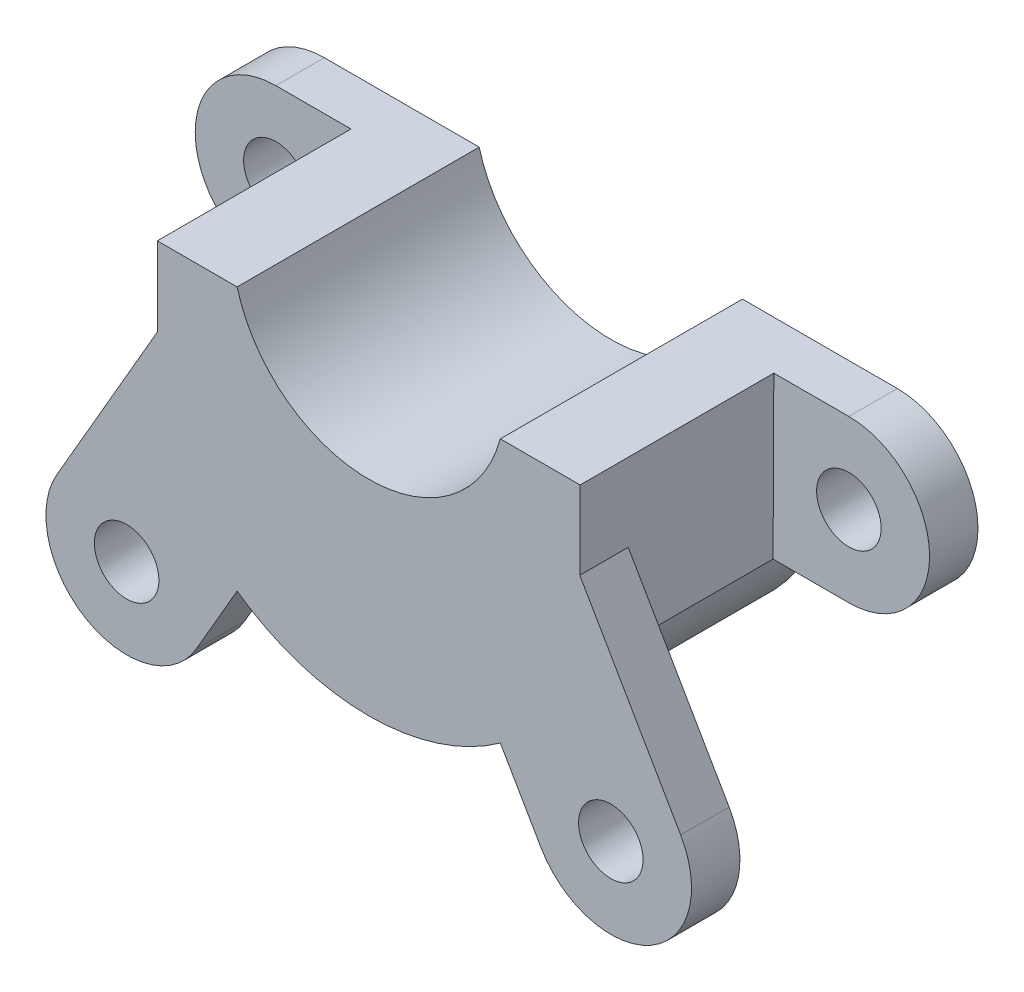
SolidWorks part; units mm, degrees
ref_plane "Plano frontal" through (0, 0, 0) normal (0, 0, 1) x (1, 0, 0)
ref_plane "Plano superior" through (0, 0, 0) normal (0, 1, 0) x (1, 0, 0)
ref_plane "Plano direito" through (0, 0, 0) normal (1, 0, 0) x (0, 0, -1)
sketch "Esboço1" plane through (0, 0, 0) normal (0, 0, 1) x (1, 0, 0)
  line L0 (-17.75, 4.941) -> (-13.0991, 4.941)
  line L1 (-17.75, -5.059) -> (-13.054, -5.059)
  line L2 (17.75, 4.941) -> (13.0991, 4.941)
  line L3 (13.054, -5.059) -> (17.75, -5.059)
  line L4 (-13.0991, 4.941) -> (-8.1548, 4.941)
  line L5 (8.1548, 4.941) -> (13.0991, 4.941)
  arc A0 (-8.1548, 4.941) -> (8.1548, 4.941) centre (0, 7.145) ccw
  circle A2 centre (-17.75, -0.059) radius 2
  circle A3 centre (17.75, -0.059) radius 2
  arc A4 (-17.75, 4.941) -> (-17.75, -5.059) centre (-17.75, -0.059) ccw
  arc A5 (17.75, -5.059) -> (17.75, 4.941) centre (17.75, -0.059) ccw
  arc A7 (-13.054, -5.059) -> (13.054, -5.059) centre (0, 0) ccw
  point P8 (0, 0)
  dimension "D4" = 4
  dimension "D3" = 35.5
extrude "Ressalto-extrusão1" add sketch "Esboço1" along normal blind 3
sketch "Esboço2" plane through (0, 0, 3) normal (0, 0, 1) x (1, 0, 0)
  line L1 (13.0991, 4.941) -> (13.054, -5.059)
  line L2 (-13.054, -5.059) -> (-13.0991, 4.941)
  line L8 (-13.0991, 4.941) -> (-8.1548, 4.941)
  line L9 (8.1548, 4.941) -> (13.0991, 4.941)
  arc A0 (-13.054, -5.059) -> (13.054, -5.059) centre (0, 0) ccw construction
  arc A2 (-13.054, -5.059) -> (13.054, -5.059) centre (0, 0) ccw
  arc A4 (-8.1548, 4.941) -> (8.1548, 4.941) centre (0, 7.145) ccw construction
  arc A5 (-8.1548, 4.941) -> (8.1548, 4.941) centre (0, 7.145) ccw
extrude "Ressalto-extrusão2" add sketch "Esboço2" along normal blind 12
sketch "Esboço3" plane through (0, 0, 15) normal (0, 0, 1) x (1, 0, 0)
  line L1 (8.1548, 4.941) -> (8.1548, -16.0857) construction
  line L2 (13.054, -5.059) -> (13.0991, 4.941) construction
  line L3 (13.0772, 0.0835) -> (8.1548, -11.3798)
  line L4 (0, 0) -> (0, 9.938) construction
  line L5 (-8.1548, 4.941) -> (-8.1548, -16.0857) construction
  line L6 (-10.6717, -15.7319) -> (-8.1548, -11.3798)
  line L7 (-19.3283, -10.7256) -> (-13.0772, 0.0835)
  line L8 (-13.0772, 0.0835) -> (-8.1548, -11.3798)
  line L11 (19.3283, -10.7256) -> (13.0772, 0.0835)
  line L16 (10.6717, -15.7319) -> (8.1548, -11.3798)
  arc A1 (-13.054, -5.059) -> (13.054, -5.059) centre (0, 0) ccw construction
  arc A2 (-10.6717, -15.7319) -> (-19.3283, -10.7256) centre (-15, -13.2288) cw
  circle A3 centre (-15, -13.2288) radius 2
  circle A6 centre (15, -13.2288) radius 2
  arc A7 (10.6717, -15.7319) -> (19.3283, -10.7256) centre (15, -13.2288) ccw
  dimension "D1" = 5
  dimension "D2" = 20
  dimension "D3" = 30
extrude "Ressalto-extrusão3" add sketch "Esboço3" against normal blind 3
